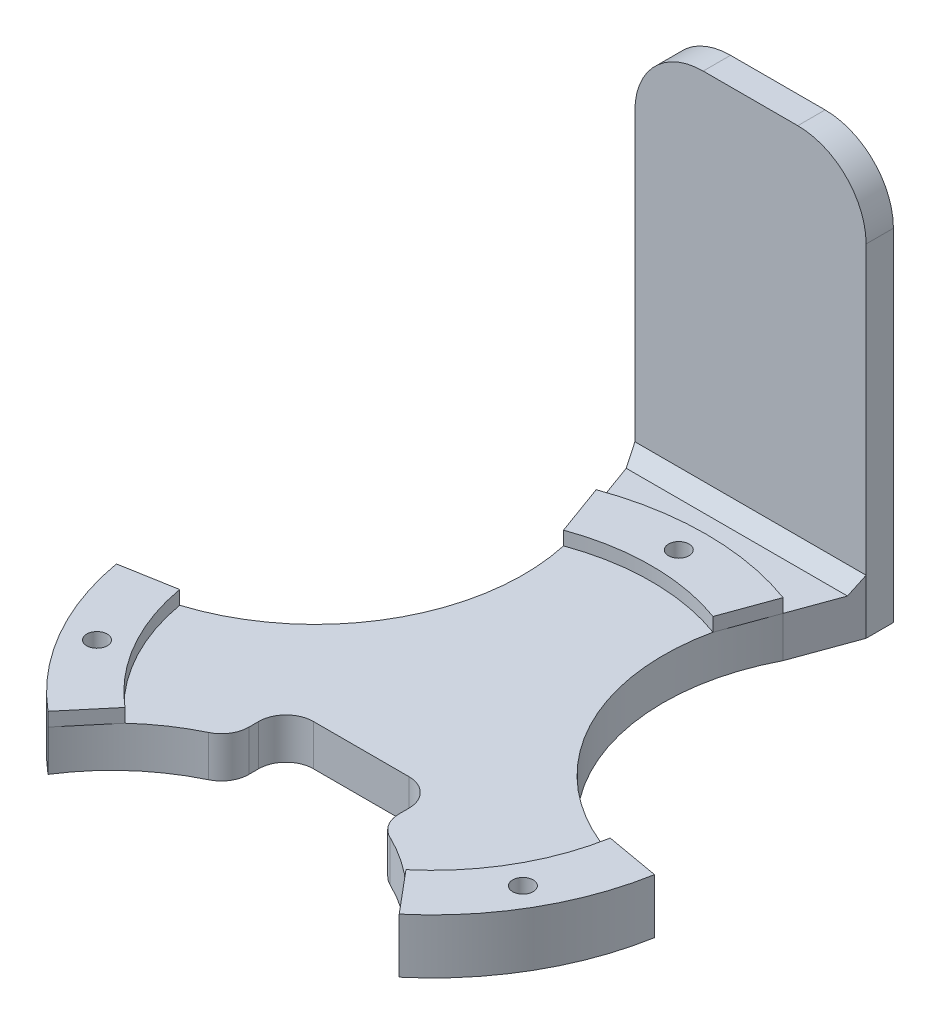
SolidWorks part; units mm, degrees
ref_plane "Front Plane" through (0, 0, 0) normal (0, 0, 1) x (1, 0, 0)
ref_plane "Top Plane" through (0, 0, 0) normal (0, 1, 0) x (1, 0, 0)
ref_plane "Right Plane" through (0, 0, 0) normal (1, 0, 0) x (0, 0, -1)
sketch "Sketch1" plane through (0, 0, 0) normal (0, 1, 0) x (1, 0, 0)
  circle A0 centre (0, 0) radius 40
  dimension "D1" = 80
extrude "Boss-Extrude1" add sketch "Sketch1" along normal blind 6
sketch "Sketch2" plane through (0, 6, 0) normal (0, 1, 0) x (1, 0, 0)
  line L0 (-13.6808, 37.5877) -> (0, 0) construction
  line L1 (0, 0) -> (13.6808, 37.5877) construction
  line L2 (0, -1000) -> (0, 49000) construction
  line L3 (-13.6808, 37.5877) -> (-10.9446, 30.0702)
  line L4 (10.9446, 30.0702) -> (13.6808, 37.5877)
  arc A0 (13.6808, 37.5877) -> (-13.6808, 37.5877) centre (0, 0) ccw
  circle A1 centre (0, 0) radius 40 construction
  arc A2 (10.9446, 30.0702) -> (-10.9446, 30.0702) centre (0, 0) ccw
  circle A3 centre (0, 36) radius 1.5
  dimension "D1" = 8
  dimension "D5" = 3
  dimension "D2" = 20
  dimension "D3" = 20
  dimension "D4" = 36
extrude "Boss-Extrude2" add sketch "Sketch2" along normal blind 2
sketch "Sketch16" plane through (0, 8, 0) normal (0, 1, 0) x (1, 0, 0)
  circle A0 centre (0, 36) radius 1.5
  circle A1 centre (0, 36) radius 1.5 construction
extrude "Cut-Extrude9" cut sketch "Sketch16" against normal through all
pattern_circular "CirPattern1" count 3 over 360 about axis through (0, 0, 0) along (0, 1, 0) of "Boss-Extrude2", "Cut-Extrude9"
sketch "Sketch5" plane through (0, 6, 0) normal (0, 1, 0) x (1, 0, 0)
  circle A1 centre (40.6986, 23.4973) radius 30.4713
extrude "Cut-Extrude3" cut sketch "Sketch5" against normal through all
pattern_circular "CirPattern2" count 3 over 360 about axis through (0, 0, 0) along (0, 1, 0) of "Cut-Extrude3"
sketch "Sketch17" plane through (0, 0, 0) normal (0, 1, 0) x (1, 0, 0)
  line L0 (-13.6808, 37.5877) -> (-16.9246, 46.5)
  line L1 (-16.9246, 46.5) -> (16.9246, 46.5)
  line L2 (16.9246, 46.5) -> (13.6808, 37.5877)
  line L3 (10.9446, 30.0702) -> (13.6808, 37.5877) construction
  line L4 (-13.6808, 37.5877) -> (-10.9446, 30.0702) construction
  line L5 (-977.7757, 44) -> (49022.2243, 44) construction
  circle A0 centre (0, 0) radius 44 construction
  arc A1 (13.6808, 37.5877) -> (-13.6808, 37.5877) centre (0, 0) ccw construction
  arc A2 (13.6808, 37.5877) -> (-13.6808, 37.5877) centre (0, 0) ccw
  dimension "D1" = 88
  dimension "D2" = 2.5
extrude "Boss-Extrude3" add sketch "Sketch17" along normal up to surface (6 mm away) up to face at (0, 6, 0)
sketch "Sketch18" plane through (0, 0, -46.5) normal (0, 0, -1) x (-1, 0, 0)
  line L0 (16.9246, 6) -> (16.9246, 0) construction
  line L1 (-16.9246, 0) -> (16.9246, 0)
  line L2 (-16.9246, 0) -> (-16.9246, 60)
  line L3 (-16.9246, 60) -> (16.9246, 60)
  line L4 (16.9246, 0) -> (16.9246, 60)
  line L5 (-16.9246, 6) -> (16.9246, 6) construction
  dimension "D1" = 54
extrude "Boss-Extrude4" add sketch "Sketch18" along normal blind 4
chamfer "Chamfer1" distance 2 angle 45 1 edges at (0, 6, -46.5)
sketch "Sketch19" plane through (0, 6, 0) normal (0, 1, 0) x (1, 0, 0)
  line L1 (11, -20.5) -> (-11, -20.5) construction
  line L2 (11, -20.5) -> (11, 7.5) construction
  line L3 (11, 7.5) -> (-11, 7.5) construction
  line L4 (-11, -20.5) -> (-11, 7.5) construction
  line L5 (11, -20.5) -> (-11, 7.5) construction
  line L6 (11, 7.5) -> (-11, -20.5) construction
  line L7 (9, -5.5) -> (-9, -5.5) construction
  line L8 (9, -5.5) -> (9, 5.5) construction
  line L9 (9, 5.5) -> (-9, 5.5) construction
  line L10 (-9, -5.5) -> (-9, 5.5) construction
  line L11 (9, -5.5) -> (-9, 5.5) construction
  line L12 (9, 5.5) -> (-9, -5.5) construction
  line L13 (-11, -20.5) -> (11, -20.5)
  line L14 (-11, -20.5) -> (-11, -10.5)
  line L15 (-11, -10.5) -> (11, -10.5)
  line L16 (11, -20.5) -> (11, -10.5)
  point P0 (0, -6.5)
  point P7 (0, 0)
  dimension "D1" = 28
  dimension "D2" = 22
  dimension "D3" = 11
  dimension "D4" = 18
  dimension "D5" = 2
  dimension "D6" = 10
extrude "Cut-Extrude10" cut sketch "Sketch19" against normal blind 25
fillet "Fillet1" radius 4 4 edges at (11, 3, 18.5781) (11, 3, 10.5) (-11, 3, 10.5) (-11, 3, 18.5781)
fillet "Fillet2" radius 10 2 edges at (16.9246, 60, -48.5) (-16.9246, 60, -48.5)
